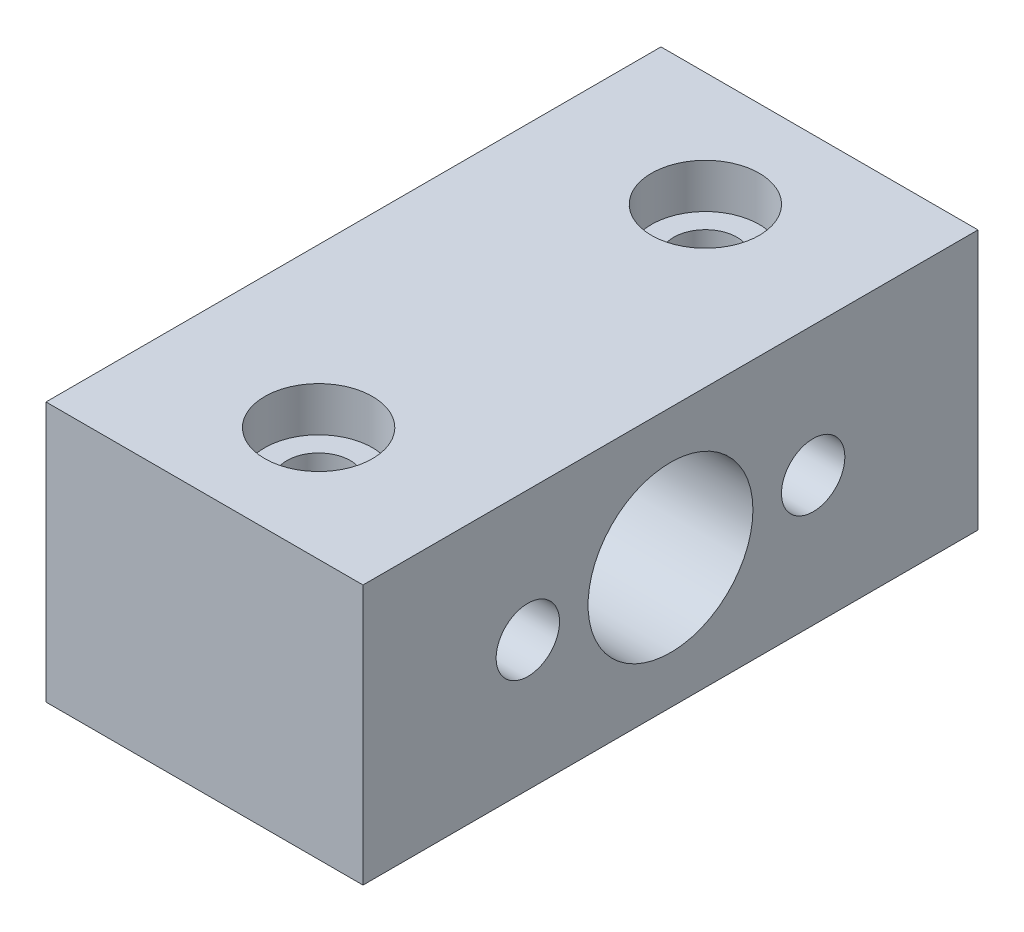
SolidWorks part; units mm, degrees
ref_plane "Plan de face" through (0, 0, 0) normal (0, 0, 1) x (1, 0, 0)
ref_plane "Plan de dessus" through (0, 0, 0) normal (0, 1, 0) x (1, 0, 0)
ref_plane "Plan de droite" through (0, 0, 0) normal (1, 0, 0) x (0, 0, -1)
sketch "Sketch1" plane through (0, 0, 0) normal (0, 0, 1) x (1, 0, 0)
  line L1 (-0.9449, 19.1713) -> (24.0551, 19.1713)
  line L2 (-0.9449, 19.1713) -> (-0.9449, -1.3287)
  line L3 (-0.9449, -1.3287) -> (24.0551, -1.3287)
  line L4 (24.0551, 19.1713) -> (24.0551, -1.3287)
  dimension "D1" = 20.5
  dimension "D2" = 25
extrude "Boss-Extrude1" add sketch "Sketch1" along normal blind 48.5
sketch "Sketch2" plane through (0, 19.1713, 0) normal (0, 1, 0) x (1, 0, 0)
  line L0 (11.5551, -48.5) -> (11.5551, 0) construction
  line L1 (24.0551, -48.5) -> (-0.9449, -48.5) construction
  line L2 (24.0551, 0) -> (-0.9449, 0) construction
  line L3 (24.0551, -48.5) -> (24.0551, 0) construction
  circle A0 centre (11.5551, -39.5) radius 4.25
  circle A1 centre (11.5551, -9) radius 4.25
  dimension "D1" = 8.5
  dimension "D2" = 8.5
  dimension "D3" = 9
  dimension "D4" = 9
extrude "Cut-Extrude1" cut sketch "Sketch2" against normal blind 3.5
sketch "Sketch3" plane through (0, 15.6713, 0) normal (0, 1, 0) x (1, 0, 0)
  circle A0 centre (11.5551, -39.5) radius 2.5
  circle A1 centre (11.5551, -9) radius 2.5
  dimension "D1" = 5
  dimension "D2" = 5
extrude "Cut-Extrude2" cut sketch "Sketch3" against normal up to surface (17 mm away) up to face at (11.5551, -1.3287, 24.25)
sketch "Sketch4" plane through (24.0551, 0, 0) normal (1, 0, 0) x (0, 0, -1)
  circle A0 centre (-24.25, 8.9213) radius 6.5
  dimension "D1" = 13
extrude "Cut-Extrude3" cut sketch "Sketch4" against normal up to surface (25 mm away) up to face at (-0.9449, 8.9213, 24.25)
sketch "Sketch5" plane through (24.0551, 0, 0) normal (1, 0, 0) x (0, 0, -1)
  circle A0 centre (-13, 8.9213) radius 2.5
  circle A1 centre (-35.5, 8.9213) radius 2.5
  circle A2 centre (-24.25, 8.9213) radius 6.5 construction
  dimension "D1" = 5
  dimension "D2" = 5
  dimension "D4" = 11.25
  dimension "D3" = 22.5
extrude "Cut-Extrude4" cut sketch "Sketch5" against normal blind 10
